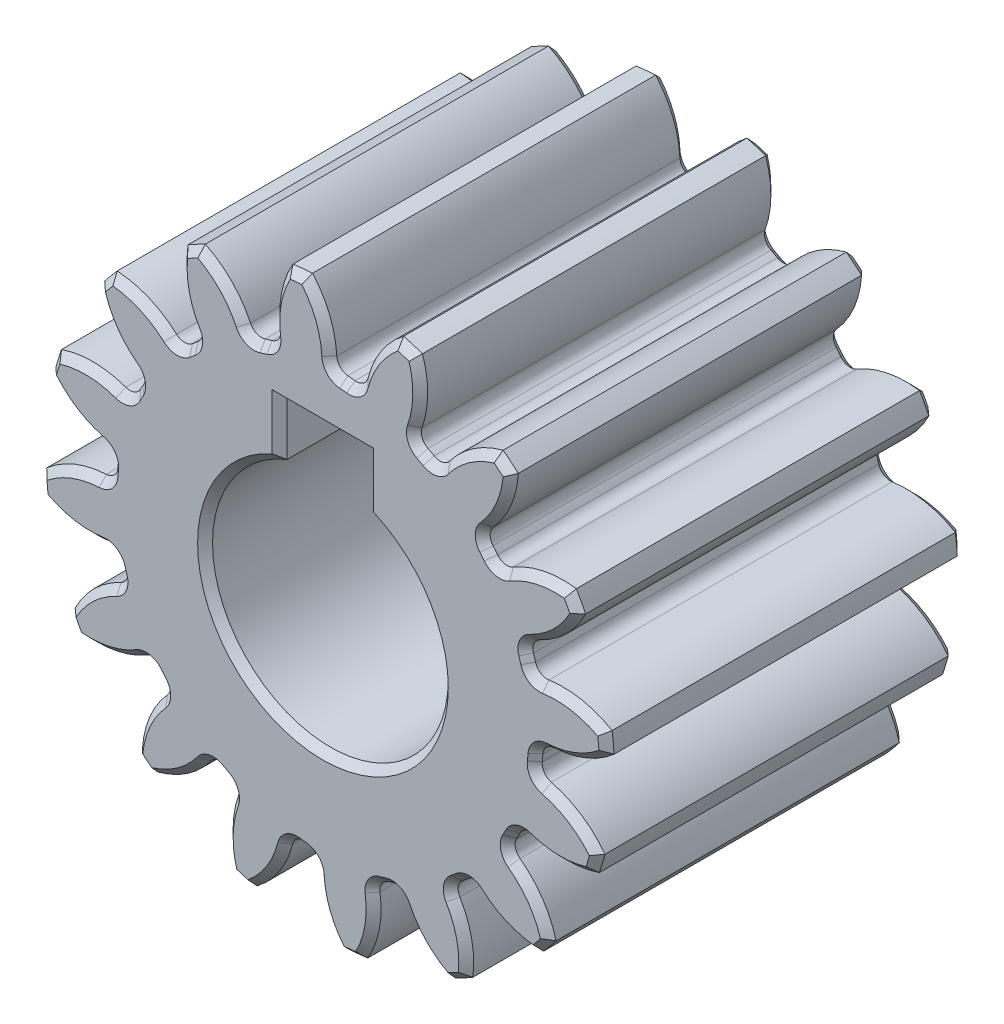
SolidWorks part; units mm, degrees
ref_plane "Front" through (0, 0, 0) normal (0, 0, 1) x (1, 0, 0)
ref_plane "Top" through (0, 0, 0) normal (0, 1, 0) x (1, 0, 0)
ref_plane "Right" through (0, 0, 0) normal (1, 0, 0) x (0, 0, -1)
sketch "Sketch3" plane through (0, 0, 0) normal (0, 0, 1) x (1, 0, 0)
  circle A0 centre (0, 0) radius 9.525
  dimension "od" = 19.05
extrude "gearBody" add sketch "Sketch3" along normal blind 12
sketch "Sketch2" plane through (0, 0, 0) normal (0, 0, 1) x (1, 0, 0)
  line L0 (0, 0) -> (7.3504, 3.0447) construction
  line L1 (9.6113, -3.1572) -> (0, 0) construction
  line L2 (0, 0) -> (36.3143, 0) construction
  line L3 (8.4666, -0.0191) -> (8.3054, -1.6447) construction
  line L5 (8.386, -0.8319) -> (0, 0) construction
  line L7 (0, 0) -> (7.9561, 0) construction
  arc A0 (7.9545, -0.1597) -> (7.8308, -1.4063) centre (0, 0) ccw construction
  arc A1 (9.5062, 0.5982) -> (9.2034, -2.4542) centre (0, 0) ccw construction
  arc A2 (8.4666, -0.0191) -> (8.3054, -1.6447) centre (0, 0) ccw construction
  arc A3 (7.098, -0.8257) -> (7.1219, -0.585) centre (0, 0) ccw
  arc A4 (9.6113, -3.1572) -> (7.4028, -1.2668) centre (6.609, -4.4295) ccw
  arc A5 (9.6113, -3.1572) -> (10.0443, 1.2073) centre (0, 0) ccw
  arc A6 (10.0443, 1.2073) -> (7.5074, -0.2123) centre (7.3504, 3.0447) cw
  arc A7 (7.1219, -0.585) -> (7.5074, -0.2123) centre (7.5269, -0.6183) cw
  arc A8 (7.4028, -1.2668) -> (7.098, -0.8257) centre (7.5017, -0.8726) cw
  point P6 (10.0443, 1.2073)
  point P22 (9.6113, -3.1572)
  dimension "baseDia" = 15.9121
  dimension "od" = 19.05
  dimension "pd" = 16.9333
  dimension "rd" = 14.2917
  dimension "rFillet" = 0.4064
  dimension "pointX" = 10.0443
  dimension "pointY" = 1.2073
  dimension "CTT" = 1.6256
  dimension "flankCenterAngle" = 22.5
extrude "toothCut" cut sketch "Sketch2" along normal through all
pattern_circular "CirPattern1" count 16 over 360 about axis through (0, 0, 0) along (0, 0, 1) of "toothCut"
sketch "hub1Dia" plane through (0, 0, 0) normal (0, 0, -1) x (-1, 0, 0)
  circle A0 centre (0, 0) radius 12.7
  dimension "hub1Dia" = 25.4
sketch "hub2Dia" plane through (0, 0, 12) normal (0, 0, 1) x (1, 0, 0)
  circle A0 centre (0, 0) radius 12.7
  dimension "hub2dia" = 25.4
sketch "boreDia" plane through (0, 0, 0) normal (0, 0, 1) x (1, 0, 0)
  circle A0 centre (0, 0) radius 3.95
  dimension "boreDia" = 7.9
extrude "bore" cut sketch "boreDia" against normal mid plane 25400
sketch "Sketch4" plane through (0, 0, 0) normal (0, 0, -1) x (-1, 0, 0)
  line L1 (-1.45, 5.45) -> (1.45, 5.45)
  line L2 (-1.45, 5.45) -> (-1.45, 2.45)
  line L3 (-1.45, 2.45) -> (1.45, 2.45)
  line L4 (1.45, 5.45) -> (1.45, 2.45)
  line L5 (-1.45, 5.45) -> (1.45, 2.45) construction
  line L6 (-1.45, 2.45) -> (1.45, 5.45) construction
  circle A0 centre (0, 0) radius 3.95 construction
  point P0 (0, 3.95)
  dimension "D1" = 2.9
  dimension "D2" = 3
extrude "Cut-Extrude1" cut sketch "Sketch4" against normal through all
sketch "Sketch5" plane through (0, 0, 0) normal (0, 0, -1) x (-1, 0, 0)
  circle A96 centre (0, 0) radius 6.3535
  arc A192 (-6.4141, -3.923) -> (-7.6725, -5.8115) centre (-4.4108, -6.6214) ccw
  arc A193 (-7.6725, -5.8115) -> (-7.1876, -6.4015) centre (0, 0) ccw
  arc A194 (-7.1876, -6.4015) -> (-5.0911, -5.5327) centre (-7.3504, -3.0447) ccw
  arc A195 (-4.687, -5.5258) -> (-5.0911, -5.5327) centre (-4.8852, -5.7595) ccw
  arc A196 (-4.687, -5.5258) -> (-4.4973, -5.6813) centre (0, 0) ccw
  arc A197 (-4.4246, -6.0789) -> (-4.4973, -5.6813) centre (-4.6875, -5.9215) ccw
  arc A198 (-4.4246, -6.0789) -> (-4.8645, -8.3052) centre (-1.5412, -7.8054) ccw
  arc A199 (-4.8645, -8.3052) -> (-4.1908, -8.6648) centre (0, 0) ccw
  arc A200 (-4.1908, -8.6648) -> (-2.5863, -7.0598) centre (-5.6258, -5.6258) ccw
  arc A201 (-2.2155, -6.8988) -> (-2.5863, -7.0598) centre (-2.3092, -7.1906) ccw
  arc A202 (-2.2155, -6.8988) -> (-1.9808, -6.9699) centre (0, 0) ccw
  arc A203 (-1.7615, -7.3094) -> (-1.9808, -6.9699) centre (-2.0646, -7.2646) ccw
  arc A204 (-1.7615, -7.3094) -> (-1.316, -9.5346) centre (1.5631, -7.801) ccw
  arc A205 (-1.316, -9.5346) -> (-0.5559, -9.6089) centre (0, 0) ccw
  arc A206 (-0.5559, -9.6089) -> (0.3122, -7.5122) centre (-3.0447, -7.3504) ccw
  arc A207 (0.5932, -7.2215) -> (0.3122, -7.5122) centre (0.6183, -7.5269) ccw
  arc A208 (0.5932, -7.2215) -> (0.8372, -7.1973) centre (0, 0) ccw
  arc A209 (1.1698, -7.4271) -> (0.8372, -7.1973) centre (0.8726, -7.5017) ccw
  arc A210 (1.1698, -7.4271) -> (2.4329, -9.3124) centre (4.4295, -6.609) ccw
  arc A211 (2.4329, -9.3124) -> (3.1636, -9.0902) centre (0, 0) ccw
  arc A212 (3.1636, -9.0902) -> (3.1632, -6.8209) centre (0, -7.9561) ccw
  arc A213 (3.3116, -6.4448) -> (3.1632, -6.8209) centre (3.4516, -6.7174) ccw
  arc A214 (3.3116, -6.4448) -> (3.5278, -6.3291) centre (0, 0) ccw
  arc A215 (3.923, -6.4141) -> (3.5278, -6.3291) centre (3.677, -6.5967) ccw
  arc A216 (3.923, -6.4141) -> (5.8115, -7.6725) centre (6.6214, -4.4108) ccw
  arc A217 (5.8115, -7.6725) -> (6.4015, -7.1876) centre (0, 0) ccw
  arc A218 (6.4015, -7.1876) -> (5.5327, -5.0911) centre (3.0447, -7.3504) ccw
  arc A219 (5.5258, -4.687) -> (5.5327, -5.0911) centre (5.7595, -4.8852) ccw
  arc A220 (5.5258, -4.687) -> (5.6813, -4.4973) centre (0, 0) ccw
  arc A221 (6.0789, -4.4246) -> (5.6813, -4.4973) centre (5.9215, -4.6875) ccw
  arc A222 (6.0789, -4.4246) -> (8.3052, -4.8645) centre (7.8054, -1.5412) ccw
  arc A223 (8.3052, -4.8645) -> (8.6648, -4.1908) centre (0, 0) ccw
  arc A224 (8.6648, -4.1908) -> (7.0598, -2.5863) centre (5.6258, -5.6258) ccw
  arc A225 (6.8988, -2.2155) -> (7.0598, -2.5863) centre (7.1906, -2.3092) ccw
  arc A226 (6.8988, -2.2155) -> (6.9699, -1.9808) centre (0, 0) ccw
  arc A227 (7.3094, -1.7615) -> (6.9699, -1.9808) centre (7.2646, -2.0646) ccw
  arc A228 (7.3094, -1.7615) -> (9.5346, -1.316) centre (7.801, 1.5631) ccw
  arc A229 (9.5346, -1.316) -> (9.6089, -0.5559) centre (0, 0) ccw
  arc A230 (9.6089, -0.5559) -> (7.5122, 0.3122) centre (7.3504, -3.0447) ccw
  arc A231 (7.2215, 0.5932) -> (7.5122, 0.3122) centre (7.5269, 0.6183) ccw
  arc A232 (7.2215, 0.5932) -> (7.1973, 0.8372) centre (0, 0) ccw
  arc A233 (7.4271, 1.1698) -> (7.1973, 0.8372) centre (7.5017, 0.8726) ccw
  arc A234 (7.4271, 1.1698) -> (9.3124, 2.4329) centre (6.609, 4.4295) ccw
  arc A235 (9.3124, 2.4329) -> (9.0902, 3.1636) centre (0, 0) ccw
  arc A236 (9.0902, 3.1636) -> (6.8209, 3.1632) centre (7.9561, 0) ccw
  arc A237 (6.4448, 3.3116) -> (6.8209, 3.1632) centre (6.7174, 3.4516) ccw
  arc A238 (6.4448, 3.3116) -> (6.3291, 3.5278) centre (0, 0) ccw
  arc A239 (6.4141, 3.923) -> (6.3291, 3.5278) centre (6.5967, 3.677) ccw
  arc A240 (6.4141, 3.923) -> (7.6725, 5.8115) centre (4.4108, 6.6214) ccw
  arc A241 (7.6725, 5.8115) -> (7.1876, 6.4015) centre (0, 0) ccw
  arc A242 (7.1876, 6.4015) -> (5.0911, 5.5327) centre (7.3504, 3.0447) ccw
  arc A243 (4.687, 5.5258) -> (5.0911, 5.5327) centre (4.8852, 5.7595) ccw
  arc A244 (4.687, 5.5258) -> (4.4973, 5.6813) centre (0, 0) ccw
  arc A245 (4.4246, 6.0789) -> (4.4973, 5.6813) centre (4.6875, 5.9215) ccw
  arc A246 (4.4246, 6.0789) -> (4.8645, 8.3052) centre (1.5412, 7.8054) ccw
  arc A247 (4.8645, 8.3052) -> (4.1908, 8.6648) centre (0, 0) ccw
  arc A248 (4.1908, 8.6648) -> (2.5863, 7.0598) centre (5.6258, 5.6258) ccw
  arc A249 (2.2155, 6.8988) -> (2.5863, 7.0598) centre (2.3092, 7.1906) ccw
  arc A250 (2.2155, 6.8988) -> (1.9808, 6.9699) centre (0, 0) ccw
  arc A251 (1.7615, 7.3094) -> (1.9808, 6.9699) centre (2.0646, 7.2646) ccw
  arc A252 (1.7615, 7.3094) -> (1.316, 9.5346) centre (-1.5631, 7.801) ccw
  arc A253 (1.316, 9.5346) -> (0.5559, 9.6089) centre (0, 0) ccw
  arc A254 (0.5559, 9.6089) -> (-0.3122, 7.5122) centre (3.0447, 7.3504) ccw
  arc A255 (-0.5932, 7.2215) -> (-0.3122, 7.5122) centre (-0.6183, 7.5269) ccw
  arc A256 (-0.5932, 7.2215) -> (-0.8372, 7.1973) centre (0, 0) ccw
  arc A257 (-1.1698, 7.4271) -> (-0.8372, 7.1973) centre (-0.8726, 7.5017) ccw
  arc A258 (-1.1698, 7.4271) -> (-2.4329, 9.3124) centre (-4.4295, 6.609) ccw
  arc A259 (-2.4329, 9.3124) -> (-3.1636, 9.0902) centre (0, 0) ccw
  arc A260 (-3.1636, 9.0902) -> (-3.1632, 6.8209) centre (0, 7.9561) ccw
  arc A261 (-3.3116, 6.4448) -> (-3.1632, 6.8209) centre (-3.4516, 6.7174) ccw
  arc A262 (-3.3116, 6.4448) -> (-3.5278, 6.3291) centre (0, 0) ccw
  arc A263 (-3.923, 6.4141) -> (-3.5278, 6.3291) centre (-3.677, 6.5967) ccw
  arc A264 (-3.923, 6.4141) -> (-5.8115, 7.6725) centre (-6.6214, 4.4108) ccw
  arc A265 (-5.8115, 7.6725) -> (-6.4015, 7.1876) centre (0, 0) ccw
  arc A266 (-6.4015, 7.1876) -> (-5.5327, 5.0911) centre (-3.0447, 7.3504) ccw
  arc A267 (-5.5258, 4.687) -> (-5.5327, 5.0911) centre (-5.7595, 4.8852) ccw
  arc A268 (-5.5258, 4.687) -> (-5.6813, 4.4973) centre (0, 0) ccw
  arc A269 (-6.0789, 4.4246) -> (-5.6813, 4.4973) centre (-5.9215, 4.6875) ccw
  arc A270 (-6.0789, 4.4246) -> (-8.3052, 4.8645) centre (-7.8054, 1.5412) ccw
  arc A271 (-8.3052, 4.8645) -> (-8.6648, 4.1908) centre (0, 0) ccw
  arc A272 (-8.6648, 4.1908) -> (-7.0598, 2.5863) centre (-5.6258, 5.6258) ccw
  arc A273 (-6.8988, 2.2155) -> (-7.0598, 2.5863) centre (-7.1906, 2.3092) ccw
  arc A274 (-6.8988, 2.2155) -> (-6.9699, 1.9808) centre (0, 0) ccw
  arc A275 (-7.3094, 1.7615) -> (-6.9699, 1.9808) centre (-7.2646, 2.0646) ccw
  arc A276 (-7.3094, 1.7615) -> (-9.5346, 1.316) centre (-7.801, -1.5631) ccw
  arc A277 (-9.5346, 1.316) -> (-9.6089, 0.5559) centre (0, 0) ccw
  arc A278 (-9.6089, 0.5559) -> (-7.5122, -0.3122) centre (-7.3504, 3.0447) ccw
  arc A279 (-7.2215, -0.5932) -> (-7.5122, -0.3122) centre (-7.5269, -0.6183) ccw
  arc A280 (-7.2215, -0.5932) -> (-7.1973, -0.8372) centre (0, 0) ccw
  arc A281 (-7.4271, -1.1698) -> (-7.1973, -0.8372) centre (-7.5017, -0.8726) ccw
  arc A282 (-7.4271, -1.1698) -> (-9.3124, -2.4329) centre (-6.609, -4.4295) ccw
  arc A283 (-9.3124, -2.4329) -> (-9.0902, -3.1636) centre (0, 0) ccw
  arc A284 (-9.0902, -3.1636) -> (-6.8209, -3.1632) centre (-7.9561, 0) ccw
  arc A285 (-6.4448, -3.3116) -> (-6.8209, -3.1632) centre (-6.7174, -3.4516) ccw
  arc A286 (-6.4448, -3.3116) -> (-6.3291, -3.5278) centre (0, 0) ccw
  arc A287 (-6.4141, -3.923) -> (-6.3291, -3.5278) centre (-6.5967, -3.677) ccw
  arc A288 (-6.4141, -3.923) -> (-7.6725, -5.8115) centre (-4.4108, -6.6214) ccw
  arc A289 (-7.6725, -5.8115) -> (-7.1876, -6.4015) centre (0, 0) ccw
  arc A290 (-7.1876, -6.4015) -> (-5.0911, -5.5327) centre (-7.3504, -3.0447) ccw
  arc A291 (-4.687, -5.5258) -> (-5.0911, -5.5327) centre (-4.8852, -5.7595) ccw
  arc A292 (-4.687, -5.5258) -> (-4.4973, -5.6813) centre (0, 0) ccw
  arc A293 (-4.4246, -6.0789) -> (-4.4973, -5.6813) centre (-4.6875, -5.9215) ccw
  arc A294 (-4.4246, -6.0789) -> (-4.8645, -8.3052) centre (-1.5412, -7.8054) ccw
  arc A295 (-4.8645, -8.3052) -> (-4.1908, -8.6648) centre (0, 0) ccw
  arc A296 (-4.1908, -8.6648) -> (-2.5863, -7.0598) centre (-5.6258, -5.6258) ccw
  arc A297 (-2.2155, -6.8988) -> (-2.5863, -7.0598) centre (-2.3092, -7.1906) ccw
  arc A298 (-2.2155, -6.8988) -> (-1.9808, -6.9699) centre (0, 0) ccw
  arc A299 (-1.7615, -7.3094) -> (-1.9808, -6.9699) centre (-2.0646, -7.2646) ccw
  arc A300 (-1.7615, -7.3094) -> (-1.316, -9.5346) centre (1.5631, -7.801) ccw
  arc A301 (-1.316, -9.5346) -> (-0.5559, -9.6089) centre (0, 0) ccw
  arc A302 (-0.5559, -9.6089) -> (0.3122, -7.5122) centre (-3.0447, -7.3504) ccw
  arc A303 (0.5932, -7.2215) -> (0.3122, -7.5122) centre (0.6183, -7.5269) ccw
  arc A304 (0.5932, -7.2215) -> (0.8372, -7.1973) centre (0, 0) ccw
  arc A305 (1.1698, -7.4271) -> (0.8372, -7.1973) centre (0.8726, -7.5017) ccw
  arc A306 (1.1698, -7.4271) -> (2.4329, -9.3124) centre (4.4295, -6.609) ccw
  arc A307 (2.4329, -9.3124) -> (3.1636, -9.0902) centre (0, 0) ccw
  arc A308 (3.1636, -9.0902) -> (3.1632, -6.8209) centre (0, -7.9561) ccw
  arc A309 (3.3116, -6.4448) -> (3.1632, -6.8209) centre (3.4516, -6.7174) ccw
  arc A310 (3.3116, -6.4448) -> (3.5278, -6.3291) centre (0, 0) ccw
  arc A311 (3.923, -6.4141) -> (3.5278, -6.3291) centre (3.677, -6.5967) ccw
  arc A312 (3.923, -6.4141) -> (5.8115, -7.6725) centre (6.6214, -4.4108) ccw
  arc A313 (5.8115, -7.6725) -> (6.4015, -7.1876) centre (0, 0) ccw
  arc A314 (6.4015, -7.1876) -> (5.5327, -5.0911) centre (3.0447, -7.3504) ccw
  arc A315 (5.5258, -4.687) -> (5.5327, -5.0911) centre (5.7595, -4.8852) ccw
  arc A316 (5.5258, -4.687) -> (5.6813, -4.4973) centre (0, 0) ccw
  arc A317 (6.0789, -4.4246) -> (5.6813, -4.4973) centre (5.9215, -4.6875) ccw
  arc A318 (6.0789, -4.4246) -> (8.3052, -4.8645) centre (7.8054, -1.5412) ccw
  arc A319 (8.3052, -4.8645) -> (8.6648, -4.1908) centre (0, 0) ccw
  arc A320 (8.6648, -4.1908) -> (7.0598, -2.5863) centre (5.6258, -5.6258) ccw
  arc A321 (6.8988, -2.2155) -> (7.0598, -2.5863) centre (7.1906, -2.3092) ccw
  arc A322 (6.8988, -2.2155) -> (6.9699, -1.9808) centre (0, 0) ccw
  arc A323 (7.3094, -1.7615) -> (6.9699, -1.9808) centre (7.2646, -2.0646) ccw
  arc A324 (7.3094, -1.7615) -> (9.5346, -1.316) centre (7.801, 1.5631) ccw
  arc A325 (9.5346, -1.316) -> (9.6089, -0.5559) centre (0, 0) ccw
  arc A326 (9.6089, -0.5559) -> (7.5122, 0.3122) centre (7.3504, -3.0447) ccw
  arc A327 (7.2215, 0.5932) -> (7.5122, 0.3122) centre (7.5269, 0.6183) ccw
  arc A328 (7.2215, 0.5932) -> (7.1973, 0.8372) centre (0, 0) ccw
  arc A329 (7.4271, 1.1698) -> (7.1973, 0.8372) centre (7.5017, 0.8726) ccw
  arc A330 (7.4271, 1.1698) -> (9.3124, 2.4329) centre (6.609, 4.4295) ccw
  arc A331 (9.3124, 2.4329) -> (9.0902, 3.1636) centre (0, 0) ccw
  arc A332 (9.0902, 3.1636) -> (6.8209, 3.1632) centre (7.9561, 0) ccw
  arc A333 (6.4448, 3.3116) -> (6.8209, 3.1632) centre (6.7174, 3.4516) ccw
  arc A334 (6.4448, 3.3116) -> (6.3291, 3.5278) centre (0, 0) ccw
  arc A335 (6.4141, 3.923) -> (6.3291, 3.5278) centre (6.5967, 3.677) ccw
  arc A336 (6.4141, 3.923) -> (7.6725, 5.8115) centre (4.4108, 6.6214) ccw
  arc A337 (7.6725, 5.8115) -> (7.1876, 6.4015) centre (0, 0) ccw
  arc A338 (7.1876, 6.4015) -> (5.0911, 5.5327) centre (7.3504, 3.0447) ccw
  arc A339 (4.687, 5.5258) -> (5.0911, 5.5327) centre (4.8852, 5.7595) ccw
  arc A340 (4.687, 5.5258) -> (4.4973, 5.6813) centre (0, 0) ccw
  arc A341 (4.4246, 6.0789) -> (4.4973, 5.6813) centre (4.6875, 5.9215) ccw
  arc A342 (4.4246, 6.0789) -> (4.8645, 8.3052) centre (1.5412, 7.8054) ccw
  arc A343 (4.8645, 8.3052) -> (4.1908, 8.6648) centre (0, 0) ccw
  arc A344 (4.1908, 8.6648) -> (2.5863, 7.0598) centre (5.6258, 5.6258) ccw
  arc A345 (2.2155, 6.8988) -> (2.5863, 7.0598) centre (2.3092, 7.1906) ccw
  arc A346 (2.2155, 6.8988) -> (1.9808, 6.9699) centre (0, 0) ccw
  arc A347 (1.7615, 7.3094) -> (1.9808, 6.9699) centre (2.0646, 7.2646) ccw
  arc A348 (1.7615, 7.3094) -> (1.316, 9.5346) centre (-1.5631, 7.801) ccw
  arc A349 (1.316, 9.5346) -> (0.5559, 9.6089) centre (0, 0) ccw
  arc A350 (0.5559, 9.6089) -> (-0.3122, 7.5122) centre (3.0447, 7.3504) ccw
  arc A351 (-0.5932, 7.2215) -> (-0.3122, 7.5122) centre (-0.6183, 7.5269) ccw
  arc A352 (-0.5932, 7.2215) -> (-0.8372, 7.1973) centre (0, 0) ccw
  arc A353 (-1.1698, 7.4271) -> (-0.8372, 7.1973) centre (-0.8726, 7.5017) ccw
  arc A354 (-1.1698, 7.4271) -> (-2.4329, 9.3124) centre (-4.4295, 6.609) ccw
  arc A355 (-2.4329, 9.3124) -> (-3.1636, 9.0902) centre (0, 0) ccw
  arc A356 (-3.1636, 9.0902) -> (-3.1632, 6.8209) centre (0, 7.9561) ccw
  arc A357 (-3.3116, 6.4448) -> (-3.1632, 6.8209) centre (-3.4516, 6.7174) ccw
  arc A358 (-3.3116, 6.4448) -> (-3.5278, 6.3291) centre (0, 0) ccw
  arc A359 (-3.923, 6.4141) -> (-3.5278, 6.3291) centre (-3.677, 6.5967) ccw
  arc A360 (-3.923, 6.4141) -> (-5.8115, 7.6725) centre (-6.6214, 4.4108) ccw
  arc A361 (-5.8115, 7.6725) -> (-6.4015, 7.1876) centre (0, 0) ccw
  arc A362 (-6.4015, 7.1876) -> (-5.5327, 5.0911) centre (-3.0447, 7.3504) ccw
  arc A363 (-5.5258, 4.687) -> (-5.5327, 5.0911) centre (-5.7595, 4.8852) ccw
  arc A364 (-5.5258, 4.687) -> (-5.6813, 4.4973) centre (0, 0) ccw
  arc A365 (-6.0789, 4.4246) -> (-5.6813, 4.4973) centre (-5.9215, 4.6875) ccw
  arc A366 (-6.0789, 4.4246) -> (-8.3052, 4.8645) centre (-7.8054, 1.5412) ccw
  arc A367 (-8.3052, 4.8645) -> (-8.6648, 4.1908) centre (0, 0) ccw
  arc A368 (-8.6648, 4.1908) -> (-7.0598, 2.5863) centre (-5.6258, 5.6258) ccw
  arc A369 (-6.8988, 2.2155) -> (-7.0598, 2.5863) centre (-7.1906, 2.3092) ccw
  arc A370 (-6.8988, 2.2155) -> (-6.9699, 1.9808) centre (0, 0) ccw
  arc A371 (-7.3094, 1.7615) -> (-6.9699, 1.9808) centre (-7.2646, 2.0646) ccw
  arc A372 (-7.3094, 1.7615) -> (-9.5346, 1.316) centre (-7.801, -1.5631) ccw
  arc A373 (-9.5346, 1.316) -> (-9.6089, 0.5559) centre (0, 0) ccw
  arc A374 (-9.6089, 0.5559) -> (-7.5122, -0.3122) centre (-7.3504, 3.0447) ccw
  arc A375 (-7.2215, -0.5932) -> (-7.5122, -0.3122) centre (-7.5269, -0.6183) ccw
  arc A376 (-7.2215, -0.5932) -> (-7.1973, -0.8372) centre (0, 0) ccw
  arc A377 (-7.4271, -1.1698) -> (-7.1973, -0.8372) centre (-7.5017, -0.8726) ccw
  arc A378 (-7.4271, -1.1698) -> (-9.3124, -2.4329) centre (-6.609, -4.4295) ccw
  arc A379 (-9.3124, -2.4329) -> (-9.0902, -3.1636) centre (0, 0) ccw
  arc A380 (-9.0902, -3.1636) -> (-6.8209, -3.1632) centre (-7.9561, 0) ccw
  arc A381 (-6.4448, -3.3116) -> (-6.8209, -3.1632) centre (-6.7174, -3.4516) ccw
  arc A382 (-6.4448, -3.3116) -> (-6.3291, -3.5278) centre (0, 0) ccw
  arc A383 (-6.4141, -3.923) -> (-6.3291, -3.5278) centre (-6.5967, -3.677) ccw
  dimension "D1" = 0.1
extrude "Boss-Extrude1" [suppressed] add sketch "Sketch5" against normal through all
chamfer "Chamfer1" distance 0.25 angle 45 200 edges at (6.0801, -6.0478, 12) (4.892, -5.3532, 12) (4.5294, -5.527, 12) (4.2877, -5.8484, 12) (4.7354, -7.1498, 12) (4.4841, -8.4035, 12) (3.3029, -7.9142, 12) (2.4711, -6.8178, 12) (2.0695, -6.8396, 12) (1.7232, -7.0441, 12) (1.6388, -8.4177, 12) (0.9269, -9.4798, 12) (0.0229, -8.5757, 12) (-0.3261, -7.2444, 12) (-0.7054, -7.111, 12) (-1.1036, -7.1673, 12) (-1.7073, -8.4041, 12) (-2.7714, -9.1129, 12) (-3.2607, -7.9317, 12) (-3.0736, -6.5682, 12) (-3.373, -6.2997, 12) (-3.7624, -6.1994, 12) (-4.7934, -7.111, 12) (-6.0478, -7.3587, 12) (-6.0478, -6.0801, 12) (-5.3532, -4.892, 12) (-5.527, -4.5294, 12) (-5.8484, -4.2877, 12) (-7.1498, -4.7354, 12) (-8.4035, -4.4841, 12) (-7.9142, -3.3029, 12) (-6.8178, -2.4711, 12) (-6.8396, -2.0695, 12) (-7.0441, -1.7232, 12) (-8.4177, -1.6388, 12) (-9.4798, -0.9269, 12) (-8.5757, -0.0229, 12) (-7.2444, 0.3261, 12) (-7.111, 0.7054, 12) (-7.1673, 1.1036, 12) (-8.4041, 1.7073, 12) (-9.1129, 2.7714, 12) (-7.9317, 3.2607, 12) (-6.5682, 3.0736, 12) (-6.2997, 3.373, 12) (-6.1994, 3.7624, 12) (-7.111, 4.7934, 12) (-7.3587, 6.0478, 12) (-6.0801, 6.0478, 12) (-4.892, 5.3532, 12) (-4.5294, 5.527, 12) (-4.2877, 5.8484, 12) (-4.7354, 7.1498, 12) (-4.4841, 8.4035, 12) (-3.3029, 7.9142, 12) (-2.4711, 6.8178, 12) (-2.0695, 6.8396, 12) (-1.7232, 7.0441, 12) (-1.6388, 8.4177, 12) (-0.9269, 9.4798, 12) (-0.0229, 8.5757, 12) (0.3261, 7.2444, 12) (0.7054, 7.111, 12) (1.1036, 7.1673, 12) (1.7073, 8.4041, 12) (2.7714, 9.1129, 12) (3.2607, 7.9317, 12) (3.0736, 6.5682, 12) (3.373, 6.2997, 12) (3.7624, 6.1994, 12) (4.7934, 7.111, 12) (6.0478, 7.3587, 12) (6.0478, 6.0801, 12) (5.3532, 4.892, 12) (5.527, 4.5294, 12) (5.8484, 4.2877, 12) (7.1498, 4.7354, 12) (8.4035, 4.4841, 12) (7.9142, 3.3029, 12) (6.8178, 2.4711, 12) (6.8396, 2.0695, 12) (7.0441, 1.7232, 12) (8.4177, 1.6388, 12) (9.4798, 0.9269, 12) (8.5757, 0.0229, 12) (7.2444, -0.3261, 12) (7.111, -0.7054, 12) (7.1673, -1.1036, 12) (8.4041, -1.7073, 12) (9.1129, -2.7714, 12) (7.9317, -3.2607, 12) (6.5682, -3.0736, 12) (6.2997, -3.373, 12) (6.1994, -3.7624, 12) (7.111, -4.7934, 12) (7.3587, -6.0478, 12) (0, -3.95, 12) (1.45, 4.5621, 12) (0, 5.45, 12) (-1.45, 4.5621, 12) (6.1994, -3.7624, 0) (6.2997, -3.373, 0) (6.5682, -3.0736, 0) (7.9317, -3.2607, 0) (9.1129, -2.7714, 0) (8.4041, -1.7073, 0) (7.1673, -1.1036, 0) (7.111, -0.7054, 0) (7.2444, -0.3261, 0) (8.5757, 0.0229, 0) (9.4798, 0.9269, 0) (8.4177, 1.6388, 0) (7.0441, 1.7232, 0) (6.8396, 2.0695, 0) (6.8178, 2.4711, 0) (7.9142, 3.3029, 0) (8.4035, 4.4841, 0) (7.1498, 4.7354, 0) (5.8484, 4.2877, 0) (5.527, 4.5294, 0) (5.3532, 4.892, 0) (6.0478, 6.0801, 0) (6.0478, 7.3587, 0) (4.7934, 7.111, 0) (3.7624, 6.1994, 0) (3.373, 6.2997, 0) (3.0736, 6.5682, 0) (3.2607, 7.9317, 0) (2.7714, 9.1129, 0) (1.7073, 8.4041, 0) (1.1036, 7.1673, 0) (0.7054, 7.111, 0) (0.3261, 7.2444, 0) (-0.0229, 8.5757, 0) (-0.9269, 9.4798, 0) (-1.6388, 8.4177, 0) (-1.7232, 7.0441, 0) (-2.0695, 6.8396, 0) (-2.4711, 6.8178, 0) (-3.3029, 7.9142, 0) (-4.4841, 8.4035, 0) (-4.7354, 7.1498, 0) (-4.2877, 5.8484, 0) (-4.5294, 5.527, 0) (-4.892, 5.3532, 0) (-6.0801, 6.0478, 0) (-7.3587, 6.0478, 0) (-7.111, 4.7934, 0) (-6.1994, 3.7624, 0) (-6.2997, 3.373, 0) (-6.5682, 3.0736, 0) (-7.9317, 3.2607, 0) (-9.1129, 2.7714, 0) (-8.4041, 1.7073, 0) (-7.1673, 1.1036, 0) (-7.111, 0.7054, 0) (-7.2444, 0.3261, 0) (-8.5757, -0.0229, 0) (-9.4798, -0.9269, 0) (-8.4177, -1.6388, 0) (-7.0441, -1.7232, 0) (-6.8396, -2.0695, 0) (-6.8178, -2.4711, 0) (-7.9142, -3.3029, 0) (-8.4035, -4.4841, 0) (-7.1498, -4.7354, 0) (-5.8484, -4.2877, 0) (-5.527, -4.5294, 0) (-5.3532, -4.892, 0) (-6.0478, -6.0801, 0) (-6.0478, -7.3587, 0) (-4.7934, -7.111, 0) (-3.7624, -6.1994, 0) (-3.373, -6.2997, 0) (-3.0736, -6.5682, 0) (-3.2607, -7.9317, 0) (-2.7714, -9.1129, 0) (-1.7073, -8.4041, 0) (-1.1036, -7.1673, 0) (-0.7054, -7.111, 0) (-0.3261, -7.2444, 0) (0.0229, -8.5757, 0) (0.9269, -9.4798, 0) (1.6388, -8.4177, 0) (1.7232, -7.0441, 0) (2.0695, -6.8396, 0) (2.4711, -6.8178, 0) (3.3029, -7.9142, 0) (4.4841, -8.4035, 0) (4.7354, -7.1498, 0) (4.2877, -5.8484, 0) (4.5294, -5.527, 0) (4.892, -5.3532, 0) (6.0801, -6.0478, 0) (7.3587, -6.0478, 0) (7.111, -4.7934, 0) (1.45, 4.5621, 0) (0, -3.95, 0) (-1.45, 4.5621, 0) (0, 5.45, 0)
